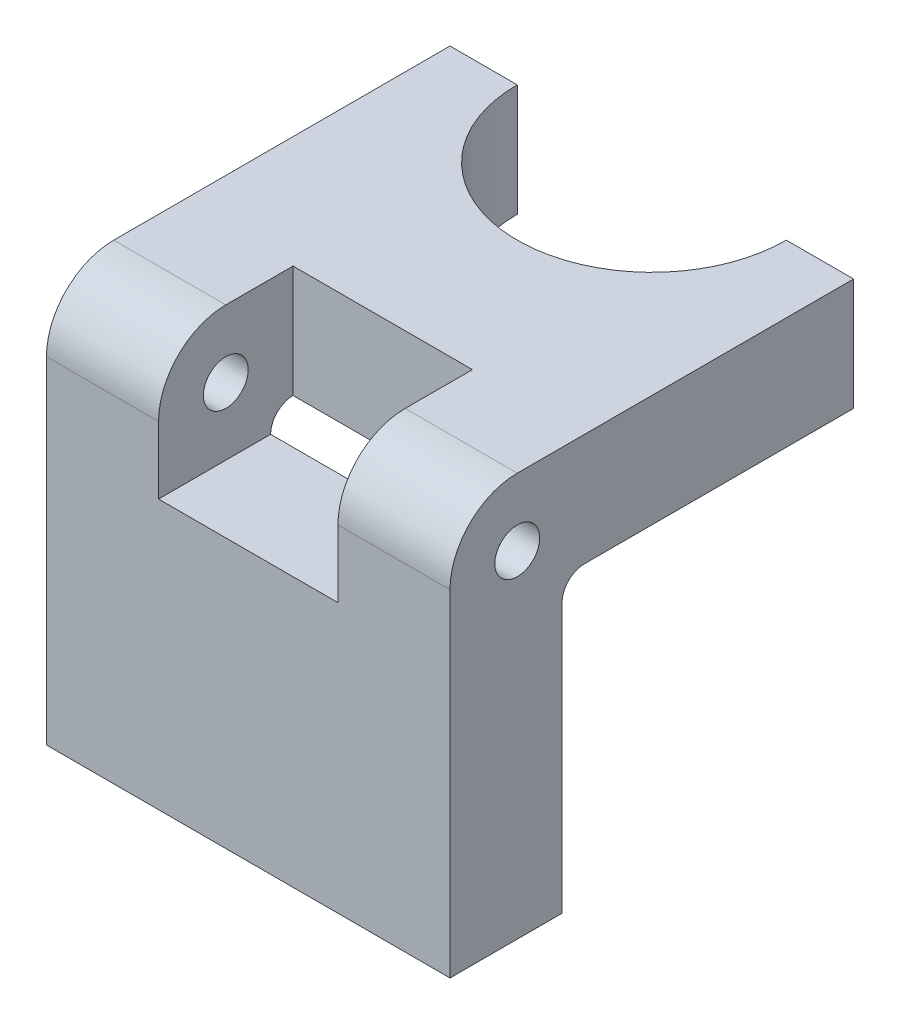
SolidWorks part; units mm, degrees
material "Nickel"
ref_plane "Front Plane" through (0, 0, 0) normal (0, 0, 1) x (1, 0, 0)
ref_plane "Top Plane" through (0, 0, 0) normal (0, 1, 0) x (1, 0, 0)
ref_plane "Right Plane" through (0, 0, 0) normal (1, 0, 0) x (0, 0, -1)
sketch "Sketch2" plane through (0, 0, 0) normal (1, 0, 0) x (0, 0, -1)
  line L0 (4.4374, -2.1585) -> (45.7124, -2.1585)
  line L1 (-1.9126, 13.7165) -> (45.7124, 13.7165)
  line L2 (-11.4376, 4.1915) -> (-11.4376, -43.4335)
  line L3 (-11.4376, -43.4335) -> (45.7124, -43.4335)
  line L4 (45.7124, 13.7165) -> (45.7124, -43.4335)
  line L5 (-1.9126, 13.7165) -> (4.4374, 13.7165)
  line L6 (-11.4376, 4.1915) -> (-11.4376, -2.1585)
  line L7 (-11.4376, -2.1585) -> (4.4374, -2.1585)
  line L8 (4.4374, 13.7165) -> (4.4374, -2.1585)
  line L9 (4.4374, -2.1585) -> (4.4374, -43.4335)
  arc A0 (-1.9126, 13.7165) -> (-11.4376, 4.1915) centre (-1.9126, 4.1915) ccw
  point P0 (-3.5001, -2.1585)
  point P12 (-3.5001, 13.5833)
  point P13 (4.4374, 5.779)
  point P14 (-11.3044, 5.779)
  dimension "D5" = 9.525
sketch "Sketch3" plane through (0, 0, 0) normal (1, 0, 0) x (0, 0, -1)
  line L4 (45.7124, 13.7165) -> (45.7124, -43.4335) construction
  line L5 (-11.4376, -43.4335) -> (45.7124, -43.4335) construction
  line L9 (4.4374, -5.3335) -> (4.4374, -2.1585)
  line L11 (4.4374, -2.1585) -> (7.6124, -2.1585)
  line L12 (45.7124, -2.1585) -> (45.7124, -43.4335)
  line L13 (4.4374, -43.4335) -> (45.7124, -43.4335)
  arc A0 (7.6124, -2.1585) -> (4.4374, -5.3335) centre (7.6124, -5.3335) ccw
  dimension "D1" = 3.175
extrude "Boss-Extrude1" add sketch "Sketch2" along normal blind 57.15
extrude "Boss-Extrude2" add sketch "Sketch3" along normal blind 57.15 contours L9 L11 A0
ref_plane "Plane1" through (0, 13.7165, 0) normal (0, 1, 0) x (1, 0, 0)
sketch "Sketch4" plane through (0, 13.7165, 0) normal (0, 1, 0) x (1, 0, 0)
  line L0 (57.15, 45.7124) -> (0, 45.7124) construction
  circle A0 centre (28.575, 45.7124) radius 19.05
  dimension "D1" = 38.1
extrude "Cut-Extrude1" cut sketch "Sketch4" against normal up to next
ref_plane "Plane2" through (41.275, 0, 0) normal (1, 0, 0) x (0, 0, -1)
sketch "Sketch5" plane through (41.275, 0, 0) normal (1, 0, 0) x (0, 0, -1)
  line L0 (7.6124, 13.7165) -> (7.6124, -2.1585)
  line L1 (-11.4376, -2.1585) -> (-11.4376, 4.1915)
  line L2 (-1.9126, 13.7165) -> (7.6124, 13.7165)
  line L4 (4.4374, -5.3335) -> (-11.4376, -5.3335)
  line L6 (7.6124, -2.1585) -> (45.7124, -2.1585)
  line L7 (45.7124, -2.1585) -> (45.7124, 13.7165)
  line L8 (45.7124, 13.7165) -> (-1.9126, 13.7165)
  line L9 (-11.4376, 4.1915) -> (-11.4376, -43.4335)
  line L10 (-11.4376, -43.4335) -> (4.4374, -43.4335)
  line L11 (4.4374, -43.4335) -> (4.4374, -5.3335)
  line L14 (7.6124, 13.7165) -> (-1.9126, 13.7165)
  line L15 (-11.4376, 4.1915) -> (-11.4376, -5.3335)
  circle A0 centre (-1.9126, 4.1915) radius 3.175
  arc A2 (7.6124, -2.1585) -> (4.4374, -5.3335) centre (7.6124, -5.3335) ccw
  arc A3 (-1.9126, 13.7165) -> (-11.4376, 4.1915) centre (-1.9126, 4.1915) ccw
  arc A4 (7.6124, -2.1585) -> (4.4374, -5.3335) centre (7.6124, -5.3335) ccw
  arc A5 (-1.9126, 13.7165) -> (-11.4376, 4.1915) centre (-1.9126, 4.1915) ccw
  dimension "D2" = 6.35
  dimension "D1" = 0
extrude "Cut-Extrude2" cut sketch "Sketch5" against normal blind 25.4 contours L2 A5 L1 L15 L4 A4 L0
ref_plane "Plane3" through (73.025, 0, 0) normal (1, 0, 0) x (0, 0, -1)
sketch "Sketch7" plane through (57.15, 0, 0) normal (1, 0, 0) x (0, 0, -1)
  circle A0 centre (-1.9126, 4.1915) radius 3.175
  dimension "D2" = 6.35
extrude "Cut-Extrude3" cut sketch "Sketch7" against normal through all contours A0
